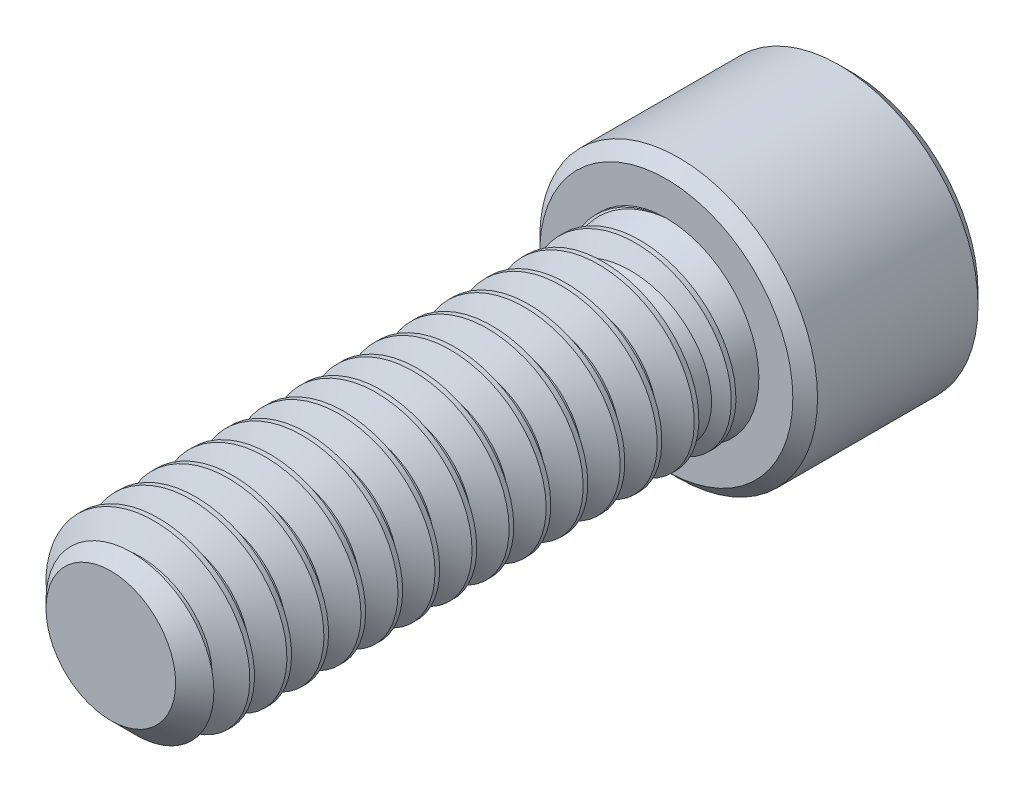
SolidWorks part; units mm, degrees
other "DetailItem1"
ref_plane "Front Plane" through (0, 0, 0) normal (0, 0, 1) x (1, 0, 0)
ref_plane "Top Plane" through (0, 0, 0) normal (0, 1, 0) x (1, 0, 0)
ref_plane "Right Plane" through (0, 0, 0) normal (1, 0, 0) x (0, 0, -1)
sketch "Sketch1" plane through (0, 0, 0) normal (1, 0, 0) x (0, 0, -1)
  line L0 (12.7, 0) -> (-12.7, 0) construction
  line L1 (-12.7, -3.175) -> (-12.7, 3.175) construction
  line L2 (12.7, 4.7625) -> (12.7, -4.7625) construction
  line L3 (6.35, 4.7625) -> (6.35, -4.7625) construction
  line L4 (12.7, 2.3813) -> (12.7, -2.3812) construction
  line L5 (-12.7, 0) -> (6.35, 0) construction
  line L6 (6.35, 3.175) -> (6.35, -3.175) construction
  line L7 (6.35, -3.175) -> (-12.7, -3.175) construction
  line L8 (-12.6206, 3.3125) -> (-13.2556, 2.2126) construction
  line L9 (-13.2556, 2.2126) -> (-13.8906, 3.3125) construction
  line L10 (-13.8906, 3.3125) -> (-12.6206, 3.3125) construction
  line L11 (-12.7, 3.175) -> (-13.8113, 3.175) construction
  line L12 (-13.1763, 2.3501) -> (-13.335, 2.3501) construction
  line L13 (-13.2556, 3.3125) -> (-13.2556, 3.175) construction
  line L14 (12.7, 4.7625) -> (6.35, 4.7625) construction
  line L15 (-13.2556, 2.3501) -> (-13.2556, 2.2126) construction
  line L16 (-13.2556, 3.2437) -> (-12.6603, 3.2437) construction
  line L17 (-13.2556, 3.2437) -> (-13.8509, 3.2437) construction
  point P10 (9.1281, 0)
  point P15 (-8.255, -3.175)
  dimension "Head Height" = 6.35
  dimension "Head Diameter" = 9.525
  dimension "Drive SIze" = 4.7625
  dimension "Drive Depth" = 3.5719
  dimension "Length" = 19.05
  dimension "Screw Size" = 6.35
  dimension "Minimum Thread Length" = 19.05
  dimension "Note" = 4.445
  dimension "D2" = 0.1588
  dimension "Pitch" = 1.27
sketch "Sketch2" plane through (0, 0, 0) normal (1, 0, 0) x (0, 0, -1)
  line L0 (12.7, 0) -> (12.7, 4.3392)
  line L1 (12.7, 4.7625) -> (6.35, 4.7625) construction
  line L2 (6.35, 4.3392) -> (6.35, 3.175)
  line L3 (6.35, 3.175) -> (-11.7475, 3.175)
  line L4 (-11.7475, 3.175) -> (-12.7, 2.2225)
  line L5 (-12.7, 2.2225) -> (-12.7, 0)
  line L6 (-12.7, 0) -> (12.7, 0)
  line L7 (12.7, 4.3392) -> (12.2767, 4.7625)
  line L8 (12.2767, 4.7625) -> (6.7733, 4.7625)
  line L9 (6.7733, 4.7625) -> (6.35, 4.3392)
  line L10 (12.7, 4.7625) -> (12.7, 4.3392) construction
  line L12 (6.35, 4.7625) -> (6.35, 4.3392) construction
  dimension "D1" = 0.9525
  dimension "D2" = 45
  dimension "D3" = 45
  dimension "D4" = 45
  dimension "D5" = 0.4233
revolve "Revolve1" add sketch "Sketch2" angle 360 about L6
sketch "Sketch3" plane through (0, 0, -12.7) normal (0, 0, -1) x (-1, 0, 0)
  line L1 (0, 2.7496) -> (-2.3813, 1.3748)
  line L2 (-2.3813, 1.3748) -> (-2.3813, -1.3748)
  line L3 (-2.3813, -1.3748) -> (0, -2.7496)
  line L4 (0, -2.7496) -> (2.3813, -1.3748)
  line L5 (2.3813, -1.3748) -> (2.3813, 1.3748)
  line L6 (2.3813, 1.3748) -> (0, 2.7496)
  circle A0 centre (0, 0) radius 2.3813 construction
extrude "Cut-Extrude1" cut sketch "Sketch3" against normal up to vertex (3.5719 mm away) up to point (0, 0, -9.1281)
sketch "Sketch4" plane through (0, 0, -12.7) normal (0, 0, -1) x (-1, 0, 0)
  circle A0 centre (0, 0) radius 2.7496
extrude "Cut-Extrude2" cut sketch "Sketch4" against normal through all draft 45
ref_plane "Plane1" through (0, 0, -6.35) normal (0, 0, 1) x (1, 0, 0)
sketch "Sketch5" plane through (0, 0, 12.7) normal (0, 0, 1) x (1, 0, 0)
  circle A0 centre (0, 0) radius 3.175
split "Split1" trim tools "Plane1" bodies to split 107 resulting bodies 113 114
curve "Helix/Spiral1" pitch 1.27 height 20.32 turns 16
sketch "Sketch6" plane through (0, 0, 0) normal (1, 0, 0) x (0, 0, -1)
  line L0 (-12.6603, 3.2437) -> (-13.8509, 3.2437)
  line L1 (-13.8509, 3.2437) -> (-13.335, 2.3501)
  line L2 (-13.335, 2.3501) -> (-13.1763, 2.3501)
  line L3 (-13.1763, 2.3501) -> (-12.6603, 3.2437)
sweep "Cut-Sweep1" cut profiles "Sketch6" path "Helix/Spiral1"
sketch "Sketch7" plane through (0, 0, -6.35) normal (0, 0, 1) x (1, 0, 0)
  circle A0 centre (0, 0) radius 3.175
extrude "Boss-Extrude1" add sketch "Sketch7" along normal up to next (19.05 mm away) draft 20
equation "\"D1\"= \"hex dia@Sketch7\" * .75"
equation "\"Drive Depth@Sketch1\" = \"Drive SIze@Sketch1\" * .75"
equation "\"D2@Sketch1\" = \"Pitch@Sketch1\" / 8"
equation "\"D1@Sketch2\" = \"Pitch@Sketch1\" * .75"
equation "\"D5@Sketch2\" = \"Head Height@Sketch1\" / 15"
equation "\"D4@Helix/Spiral1\" = \"Pitch@Sketch1\""
equation "\"D3@Helix/Spiral1\" = \"Minimum Thread Length@Sketch1\" + \"Pitch@Sketch1\""
equation "\"Note@Sketch1\"=\"Pitch@Sketch1\"*3.5"
